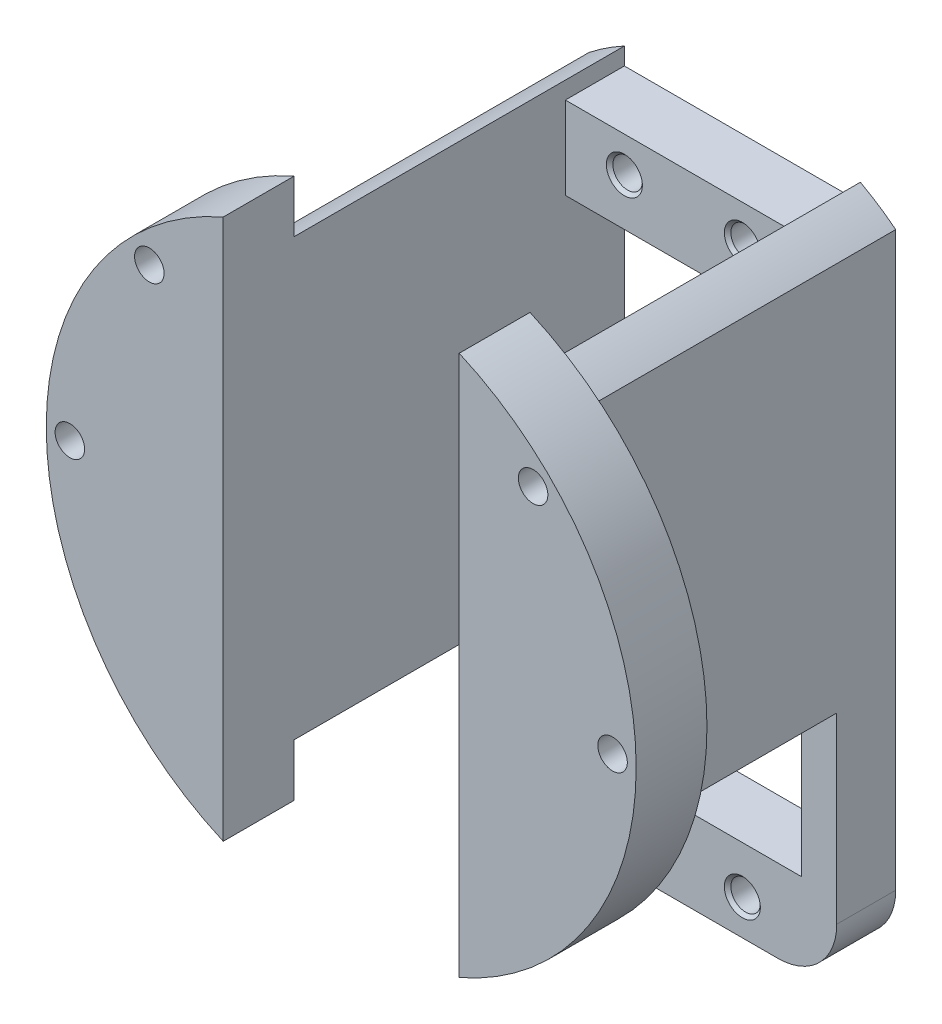
SolidWorks part; units mm, degrees
material "ПК/АБС"
ref_plane "Спереди" through (0, 0, 0) normal (0, 0, 1) x (1, 0, 0)
ref_plane "Сверху" through (0, 0, 0) normal (0, 1, 0) x (1, 0, 0)
ref_plane "Справа" through (0, 0, 0) normal (1, 0, 0) x (0, 0, -1)
sketch "Эскиз1" plane through (0, 0, 0) normal (0, 0, 1) x (1, 0, 0)
  line L0 (0, 0) -> (0, 23258.0729) construction
  line L1 (0, 0) -> (23258.0729, 0) construction
  line L2 (-10, 10) -> (10, 10)
  line L3 (10, 10) -> (10, -30)
  line L4 (10, -30) -> (-10, -30)
  line L5 (-10, -30) -> (-10, 10)
  line L6 (-13, 17) -> (13, 17)
  line L7 (13, 17) -> (13, -37)
  line L8 (13, -37) -> (-13, -37)
  line L9 (-13, -37) -> (-13, 17)
  point P7 (0, -30)
  dimension "D1" = 20
  dimension "D2" = 40
  dimension "D3" = 10
  dimension "D4" = 7
  dimension "D5" = 7
  dimension "D6" = 3
  dimension "D7" = 3
extrude "Бобышка-Вытянуть1" add sketch "Эскиз1" along normal blind 5
sketch "Эскиз2" plane through (0, 0, 0) normal (0, 0, 1) x (1, 0, 0)
  line L0 (10, -18.4662) -> (10, 18.4662)
  line L1 (10, -30) -> (10, 10) construction
  line L2 (-10, -18.4662) -> (-10, 18.4662)
  line L3 (-10, 10) -> (-10, -30) construction
  line L4 (-13, -16.4924) -> (-13, 16.4924)
  line L5 (-13, 17) -> (-13, -37) construction
  line L6 (13, 16.4924) -> (13, -16.4924)
  line L7 (13, -37) -> (13, 17) construction
  arc A0 (-10, 18.4662) -> (-13, 16.4924) centre (0, 0) ccw
  arc A1 (10, -18.4662) -> (13, -16.4924) centre (0, 0) ccw
  arc A2 (-13, -16.4924) -> (-10, -18.4662) centre (0, 0) ccw
  arc A3 (13, 16.4924) -> (10, 18.4662) centre (0, 0) ccw
  dimension "D1" = 42
extrude "Бобышка-Вытянуть2" add sketch "Эскиз2" along normal blind 28
sketch "Эскиз3" plane through (0, 0, 28) normal (0, 0, 1) x (1, 0, 0)
  line L0 (-21, 0) -> (21, 0) construction
  line L1 (-13, -21.3826) -> (-13, -50021.3826) construction
  line L2 (-13, -16.4924) -> (-13, -37) construction
  line L3 (13, -21.1704) -> (13, -50021.1704) construction
  line L4 (13, -37) -> (13, -16.4924) construction
  line L5 (-13, -16.4924) -> (-13, -37)
  line L6 (-13, -37) -> (13, -37)
  line L7 (13, -37) -> (13, -16.4924)
  circle A0 centre (0, 0) radius 21 construction
  arc A10 (-13, -16.4924) -> (13, -16.4924) centre (0, 0) cw
  point P9 (-13, -26.7462)
  point P16 (13, -26.7462)
  point P25 (0, 0)
  dimension "D2" = 42
extrude "Вырез-Вытянуть1" cut sketch "Эскиз3" against normal through all flip side to cut
fillet "Скругление1" radius 5 2 edges at (-13, -37, 2.5) (13, -37, 2.5)
sketch "Эскиз7" plane through (0, 0, 28) normal (0, 0, 1) x (1, 0, 0)
  line L2 (-10, -22.9129) -> (-10, 22.9129)
  line L3 (10, -22.9129) -> (10, 22.9129)
  line L4 (10, -30) -> (10, -18.4662) construction
  line L5 (-10, -18.4662) -> (-10, -30) construction
  arc A2 (-10, 22.9129) -> (-10, -22.9129) centre (0, 0) ccw
  arc A3 (10, -22.9129) -> (10, 22.9129) centre (0, 0) ccw
  dimension "D1" = 50
extrude "Бобышка-Вытянуть3" add sketch "Эскиз7" along normal blind 6
hole_wizard "Отверстие обработанное метчиком M3x0.51" positions "Эскиз4" profile "Эскиз5" tap size "M3x0.5" standard "HASCO Metric" end condition through all
sketch "Эскиз4" plane through (0, 0, 5) normal (0, 0, 1) x (1, 0, 0)
  line L0 (0, 0) -> (0, 50000) construction
  line L1 (0, -10) -> (-50000, -10) construction
  line L2 (10, 10) -> (-10, 10) construction
  line L4 (0, 14) -> (-50000, 14) construction
  line L5 (-5, -10) -> (-5, 49990) construction
  point P0 (-5, 14)
  dimension "D1" = 20
  dimension "D2" = 24
  dimension "D3" = 5
sketch "Эскиз5" plane through (-5, 14, 5) normal (1, 0, 0) x (0, -1, 0)
  line L0 (0, 0) -> (0, 5)
  line L1 (0, 5) -> (1.25, 5)
  line L2 (1.25, 5) -> (1.25, 0.275)
  line L3 (1.25, 0.275) -> (1.525, 0)
  line L5 (1.525, 0) -> (0, 0)
  line L6 (-1.25, 0.275) -> (-1.525, 0) construction
  line L11 (0, -6.35) -> (0, 107.95) construction
  dimension "Диаметр проходного сверла" = 2.5
  dimension "Глубина проходного сверла" = 5
  dimension "Диаметр передней зенковки" = 3.05
  dimension "Угол передней зенковки" = 90
cosmetic thread "Отверстие резьбы1" parameters "D2"=3
pattern_linear "Линейный массив1" count 2 spacing 10 along (1, 0, 0) count 2 spacing 48 along (0, -1, 0) of "Отверстие обработанное метчиком M3x0.51"
hole_wizard "Отверстие1" positions "Эскиз8" profile "Эскиз9" legacy end condition through all
sketch "Эскиз8" plane through (0, 0, 34) normal (0, 0, 1) x (1, 0, 0)
  line L0 (-23, 0) -> (23, 0) construction
  circle A0 centre (0, 0) radius 23 construction
  point P0 (-23, 0)
  dimension "D1" = 46
sketch "Эскиз9" plane through (-23, 0, 34) normal (1, 0, 0) x (0, -1, 0)
  line L0 (0, 0) -> (0, 34)
  line L1 (0, 34) -> (1.25, 34)
  line L2 (1.25, 34) -> (1.25, 0)
  line L3 (1.25, 0) -> (0, 0)
  line L4 (0, 110) -> (0, -10) construction
  dimension "Диаметр" = 2.5
  dimension "Глубина" = 34
pattern_circular "Круговой массив1" count 8 over 360 about axis through (0, 0, 34) along (0, 0, 1) skipping 1, 2, 3, 6 of "Отверстие1"
